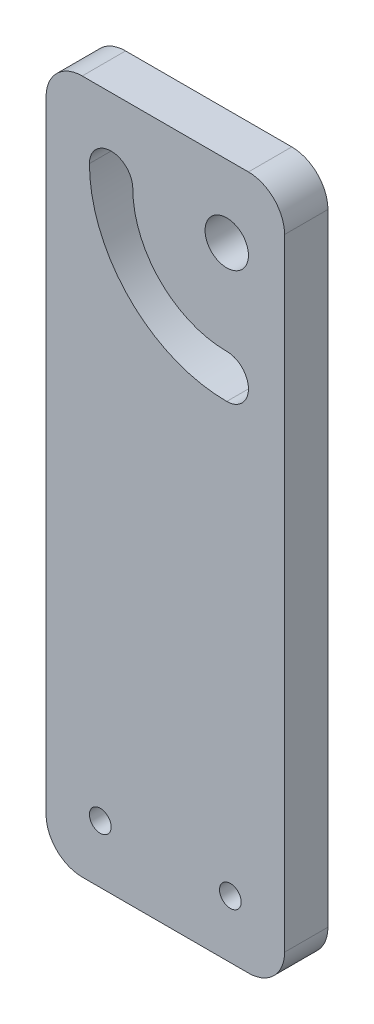
SolidWorks part; units mm, degrees
other "Marcação1"
sketch "Esboço5" plane through (0, 50, 68.25) normal (-0.797, 0.1637, 0.5813) x (0.5636, -0.1442, 0.8134)
material "MDF"
ref_plane "Plano frontal" through (0, 0, 0) normal (0, 0, 1) x (1, 0, 0)
ref_plane "Plano superior" through (0, 0, 0) normal (0, 1, 0) x (1, 0, 0)
ref_plane "Plano direito" through (0, 0, 0) normal (1, 0, 0) x (0, 0, -1)
sketch "Esboço1" plane through (0, 0, 0) normal (0, 0, 1) x (1, 0, 0)
  line L1 (5, 50) -> (28, 50)
  line L4 (25, 40) -> (25, 37) construction
  line L6 (28, -46) -> (5, -46)
  line L8 (33, 45) -> (33, -41)
  line L9 (0, 45) -> (0, -41)
  line L10 (16.5, -46) -> (16.5, -17.8421) construction
  line L11 (0, 16.5) -> (33, 16.5) construction
  circle A0 centre (25, 40) radius 3
  arc A2 (25, 24) -> (9, 40) centre (25, 40) cw construction
  arc A3 (6, 40) -> (25, 21) centre (25, 40) ccw
  arc A4 (12, 40) -> (25, 27) centre (25, 40) ccw
  arc A5 (12, 40) -> (6, 40) centre (9, 40) ccw
  arc A6 (25, 21) -> (25, 27) centre (25, 24) ccw
  circle A7 centre (25.5, -38) radius 1.5
  circle A8 centre (7.5, -38) radius 1.5
  arc A9 (5, -46) -> (0, -41) centre (5, -41) cw
  arc A10 (0, 45) -> (5, 50) centre (5, 45) cw
  arc A11 (33, -41) -> (28, -46) centre (28, -41) cw
  arc A12 (28, 50) -> (33, 45) centre (28, 45) cw
  point P10 (13.6863, 28.6863)
  point P25 (0, 50)
  point P28 (33, -46)
  point P31 (33, 50)
  dimension "D3" = 6
  dimension "D5" = 16
  dimension "D6" = 13
  dimension "D2" = 3
  dimension "D4" = 8
  dimension "D8" = 7.5
  dimension "D9" = 5
  dimension "D1" = 96
  dimension "D7" = 33
  dimension "D10" = 67
extrude "Ressalto-extrusão2" add sketch "Esboço1" along normal blind 6
